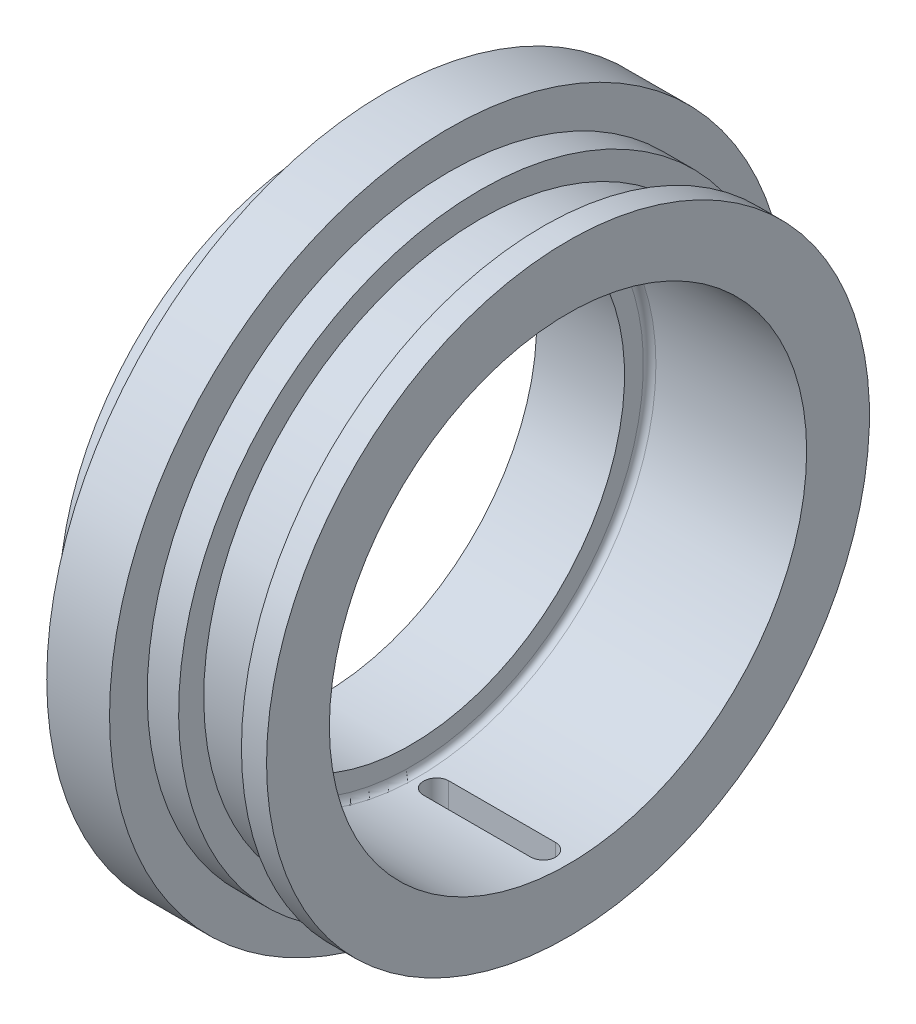
SolidWorks part; units mm, degrees
ref_plane "Přední rovina" through (0, 0, 0) normal (0, 0, 1) x (1, 0, 0)
ref_plane "Horní rovina" through (0, 0, 0) normal (0, 1, 0) x (1, 0, 0)
ref_plane "Pravá rovina" through (0, 0, 0) normal (1, 0, 0) x (0, 0, -1)
sketch "Skica1" plane through (0, 0, 0) normal (0, 0, 1) x (1, 0, 0)
  line L0 (-351.05, 19) -> (-362.55, 19) construction
  line L2 (-346.55, 24) -> (-360.05, 24) construction
  line L3 (-351.05, 19) -> (-362.55, 19) construction
  line L4 (-346.55, 24) -> (-353.05, 24) construction
  line L5 (-379.9367, 0) -> (-341.809, 0) construction
  line L6 (-351.05, 24) -> (-353.05, 24)
  line L7 (-360.55, 24) -> (-360.55, 27)
  line L9 (-360.55, 27) -> (-365.55, 27)
  line L10 (-365.55, 27) -> (-365.55, 20)
  line L11 (-363.55, 19) -> (-351.05, 19)
  line L12 (-351.05, 19) -> (-351.05, 24)
  line L13 (-365.55, -21) -> (-365.55, 21) construction
  line L14 (-353.05, 24) -> (-353.05, 22)
  line L15 (-353.05, 22) -> (-358.05, 22)
  line L16 (-358.05, 22) -> (-358.05, 24)
  line L17 (-358.05, 24) -> (-360.55, 24) construction
  line L18 (-358.05, 24) -> (-360.55, 24)
  line L19 (-365.55, 20) -> (-367.05, 20)
  line L20 (-367.05, 20) -> (-367.55, 21)
  line L21 (-367.55, 21) -> (-370.55, 21)
  line L22 (-370.55, 21) -> (-370.55, 19)
  line L23 (-370.55, 19) -> (-363.55, 19) construction
  line L25 (-363.55, 17.9) -> (-363.55, -17.9) construction
  line L26 (-363.55, 19) -> (-363.55, 17)
  line L27 (-363.55, 17) -> (-370.55, 17)
  line L28 (-370.55, 17) -> (-370.55, 19)
  line L29 (-363.55, 17.9) -> (-363.55, -17.9) construction
  line L30 (-360.55, 27) -> (-360.55, -27) construction
  line L31 (-360.55, 27) -> (-360.55, -27) construction
  dimension "D1" = 5
  dimension "D2" = 2
  dimension "D3" = 2
  dimension "D4" = 5
  dimension "D5" = 21
  dimension "D6" = 4
  dimension "D7" = 1
  dimension "D8" = 2
  dimension "D9" = 1.5
revolve "Rotovat1" add sketch "Skica1" angle 360 about L5
cosmetic thread "Kosmetický závit1" parameters "D1"=5, "D2"=40.773
cosmetic thread "Kosmetický závit2" parameters "D2"=40.773
fillet "Zaoblit1" radius 0.5 1 edges at (-363.55, 0, 19)
ref_plane "Rovina2" through (0, -19, 0) normal (0, 1, 0) x (1, 0, 0)
sketch "Skica3" plane through (0, -19, 0) normal (0, 1, 0) x (1, 0, 0)
  line L1 (-361.55, 0) -> (-353.05, 0) construction
  line L2 (-353.05, 0) -> (-361.55, 0) construction
  line L3 (-353.05, -1) -> (-361.55, -1)
  line L4 (-353.05, 1) -> (-361.55, 1)
  line L5 (-351.05, -19) -> (-351.05, 19) construction
  line L6 (-10.725, 0) -> (10.725, 0) construction
  arc A0 (-353.05, -1) -> (-353.05, 1) centre (-353.05, 0) ccw
  arc A1 (-361.55, 1) -> (-361.55, -1) centre (-361.55, 0) ccw
  point P2 (-357.3, 0)
  dimension "D1" = 2
  dimension "D2" = 2
  dimension "D3" = 8.5
extrude "Odebrat vysunutím2" cut sketch "Skica3" against normal up to next and the other way up to next
